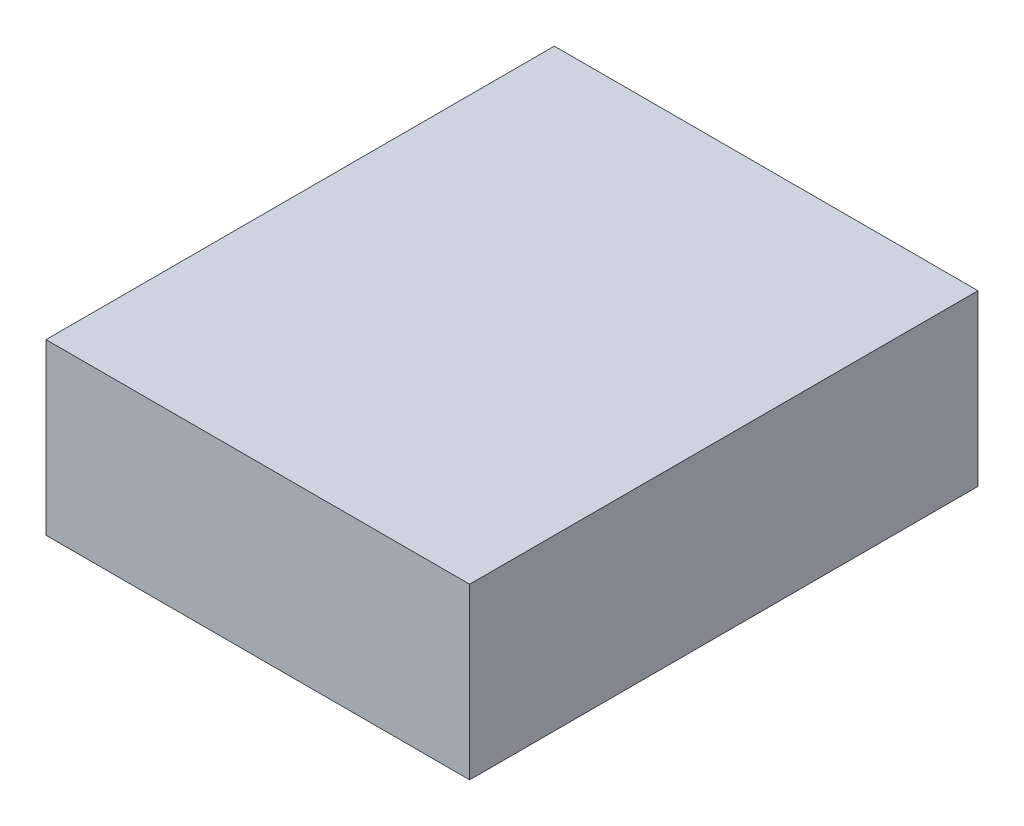
SolidWorks part; units mm, degrees
ref_plane "Front Plane" through (0, 0, 0) normal (0, 0, 1) x (1, 0, 0)
ref_plane "Top Plane" through (0, 0, 0) normal (0, 1, 0) x (1, 0, 0)
ref_plane "Right Plane" through (0, 0, 0) normal (1, 0, 0) x (0, 0, -1)
sketch "Sketch1" plane through (0, 0, 0) normal (0, 1, 0) x (1, 0, 0)
  line L1 (0, 0) -> (2.5, 0)
  line L2 (0, 0) -> (0, 3)
  line L3 (0, 3) -> (2.5, 3)
  line L4 (2.5, 0) -> (2.5, 3)
  dimension "D1" = 2.5
  dimension "D2" = 3
extrude "Boss-Extrude1" add sketch "Sketch1" along normal blind 1
